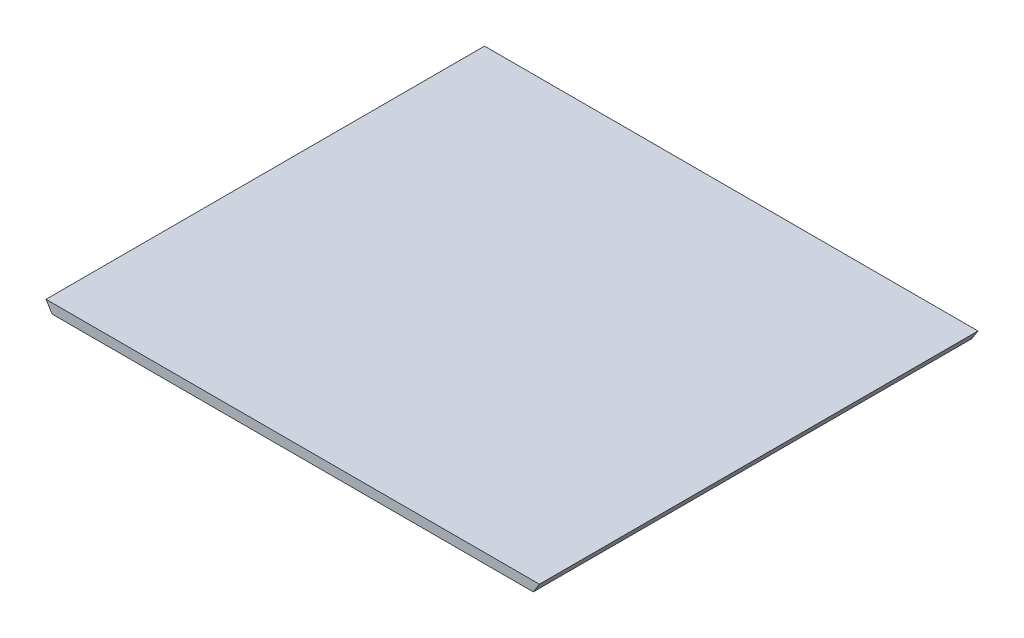
SolidWorks part; units mm, degrees
ref_plane "Ebene vorne" through (0, 0, 0) normal (0, 0, 1) x (1, 0, 0)
ref_plane "Ebene oben" through (0, 0, 0) normal (0, 1, 0) x (1, 0, 0)
ref_plane "Ebene rechts" through (0, 0, 0) normal (1, 0, 0) x (0, 0, -1)
sketch "Skizze1" plane through (0, 0, 0) normal (0, 0, 1) x (1, 0, 0)
  line L0 (-253.157, 264.0237) -> (-246.8583, 254.0237)
  line L1 (253.157, 264.0237) -> (246.8583, 254.0237)
  line L15 (253.157, 264.0237) -> (-253.157, 264.0237)
  line L22 (-246.8583, 254.0237) -> (246.8583, 254.0237)
extrude "Aufsatz-Linear austragen1" add sketch "Skizze1" along normal blind 450
